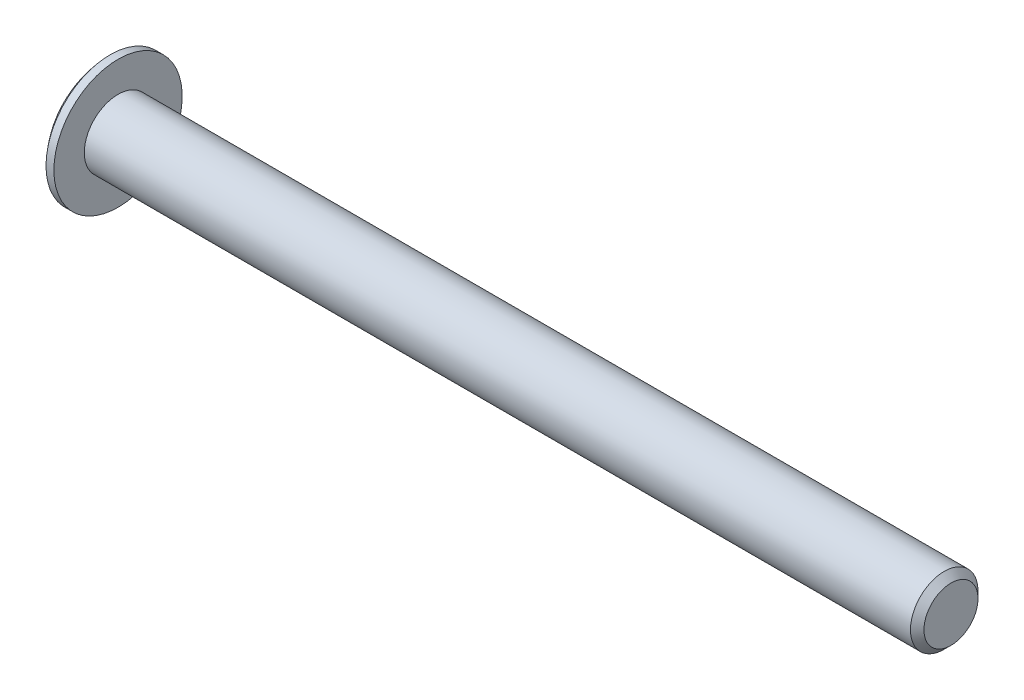
SolidWorks part; units mm, degrees
ref_plane "Front Plane" through (0, 0, 0) normal (0, 0, 1) x (1, 0, 0)
ref_plane "Top Plane" through (0, 0, 0) normal (0, 1, 0) x (1, 0, 0)
ref_plane "Right Plane" through (0, 0, 0) normal (1, 0, 0) x (0, 0, -1)
sketch "Sketch1" plane through (0, 0, 0) normal (0, 0, 1) x (1, 0, 0)
  line L0 (0, 0) -> (76.3, 0)
  line L1 (0, 0) -> (0, 2.86)
  line L2 (1.6, 5.7) -> (2.3, 5.7)
  line L3 (2.3, 5.7) -> (2.3, 3)
  line L4 (2.3, 3) -> (76.3, 3)
  line L5 (76.3, 3) -> (76.3, 0)
  arc A1 (0, 2.86) -> (1.6, 5.7) centre (6.7311, 0.9385) cw
  dimension "D7" = 7
  dimension "D1" = 74
  dimension "D2" = 3
  dimension "D3" = 2.86
  dimension "D4" = 0.7
  dimension "D5" = 2.3
  dimension "D6" = 5.7
revolve "Revolve1" add sketch "Sketch1" angle 360 about L0
chamfer "Chamfer1" distance 0.6 angle 45 1 edges at (76.3, 0, 3)
sketch "Sketch2" plane through (0, 0, 0) normal (-1, 0, 0) x (0, 0, 1)
  line L1 (0, 2.3094) -> (-2, 1.1547)
  line L2 (-2, 1.1547) -> (-2, -1.1547)
  line L3 (-2, -1.1547) -> (0, -2.3094)
  line L4 (0, -2.3094) -> (2, -1.1547)
  line L5 (2, -1.1547) -> (2, 1.1547)
  line L6 (2, 1.1547) -> (0, 2.3094)
  circle A0 centre (0, 0) radius 2 construction
  dimension "D1" = 4
extrude "Cut-Extrude1" cut sketch "Sketch2" against normal blind 2
